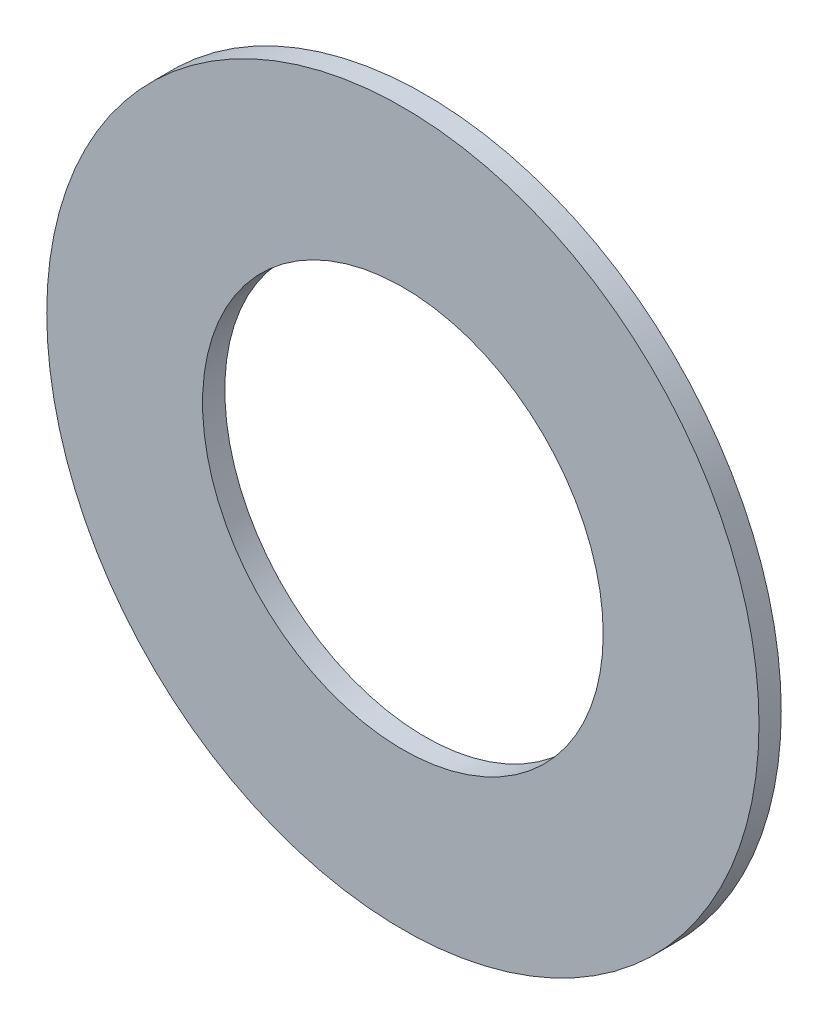
SolidWorks part; units mm, degrees
ref_plane "Front Plane" through (0, 0, 0) normal (0, 0, 1) x (1, 0, 0)
ref_plane "Top Plane" through (0, 0, 0) normal (0, 1, 0) x (1, 0, 0)
ref_plane "Right Plane" through (0, 0, 0) normal (1, 0, 0) x (0, 0, -1)
sketch "Sketch1" plane through (0, 0, 0) normal (0, 0, 1) x (1, 0, 0)
  circle A0 centre (0, 0) radius 8
  circle A1 centre (0, 0) radius 4.5
  dimension "D1" = 16
  dimension "D2" = 9
extrude "Boss-Extrude1" add sketch "Sketch1" along normal blind 0.5
